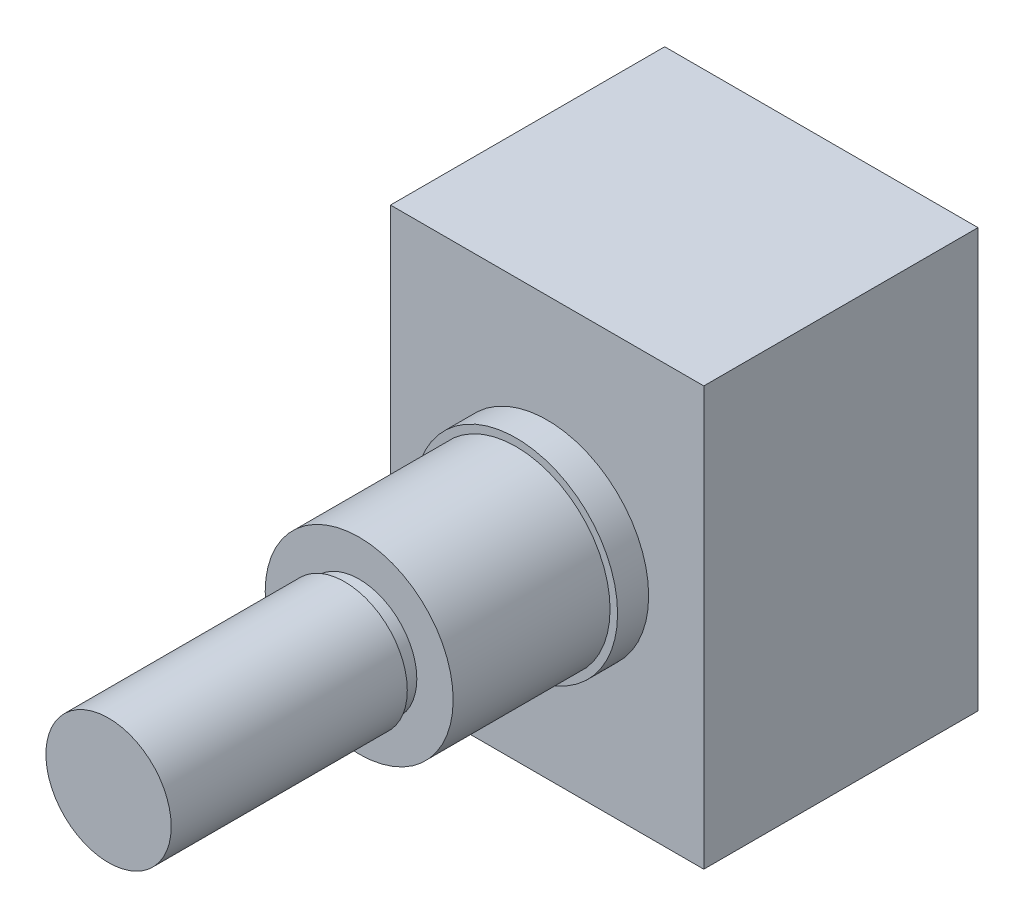
SolidWorks part; units mm, degrees
material "6061-T6 (SS)"
ref_plane "Front Plane" through (0, 0, 0) normal (0, 0, 1) x (1, 0, 0)
ref_plane "Top Plane" through (0, 0, 0) normal (0, 1, 0) x (1, 0, 0)
ref_plane "Right Plane" through (0, 0, 0) normal (1, 0, 0) x (0, 0, -1)
sketch "Sketch1" plane through (0, 0, 0) normal (0, 0, 1) x (1, 0, 0)
  line L1 (-7.9375, -10.6045) -> (7.9375, -10.6045)
  line L2 (-7.9375, -10.6045) -> (-7.9375, 10.6045)
  line L3 (-7.9375, 10.6045) -> (7.9375, 10.6045)
  line L4 (7.9375, -10.6045) -> (7.9375, 10.6045)
  line L5 (-7.9375, -10.6045) -> (7.9375, 10.6045) construction
  line L6 (-7.9375, 10.6045) -> (7.9375, -10.6045) construction
  point P0 (0, 0)
  dimension "D1" = 21.209
  dimension "D2" = 15.875
extrude "Boss-Extrude1" add sketch "Sketch1" along normal blind 13.8938
sketch "Sketch2" plane through (0, 0, 13.8938) normal (0, 0, 1) x (1, 0, 0)
  circle A0 centre (0, 0) radius 5.1435
  dimension "D1" = 10.287
extrude "Boss-Extrude2" add sketch "Sketch2" along normal blind 1.5748
sketch "Sketch3" plane through (0, 0, 13.8938) normal (0, 0, 1) x (1, 0, 0)
  circle A0 centre (0, 0) radius 4.7625
  dimension "D1" = 9.525
extrude "Boss-Extrude3" add sketch "Sketch3" along normal blind 9.525
sketch "Sketch4" plane through (0, 0, 13.8938) normal (0, 0, 1) x (1, 0, 0)
  circle A0 centre (0, 0) radius 3.175
  dimension "D1" = 6.35
extrude "Boss-Extrude4" add sketch "Sketch4" along normal blind 22.225
sketch "Sketch5" plane through (0, 0, 0) normal (0, 1, 0) x (1, 0, 0)
  line L0 (3.175, -36.1188) -> (3.175, -23.4188) construction
  line L1 (3.175, -23.4188) -> (2.921, -23.4188)
  line L2 (3.175, -23.4188) -> (3.175, -24.1554)
  line L3 (3.175, -24.1554) -> (2.921, -24.1554)
  line L4 (2.921, -23.4188) -> (2.921, -24.1554)
  line L5 (0, -36.1188) -> (0, -25.3753) construction
  line L6 (-3.175, -36.1188) -> (3.175, -36.1188) construction
  line L7 (-3.175, -23.4188) -> (3.175, -23.4188) construction
  dimension "D1" = 2.921
  dimension "D2" = 0.7366
revolve "Cut-Revolve1" cut sketch "Sketch5" angle 360 about L5
